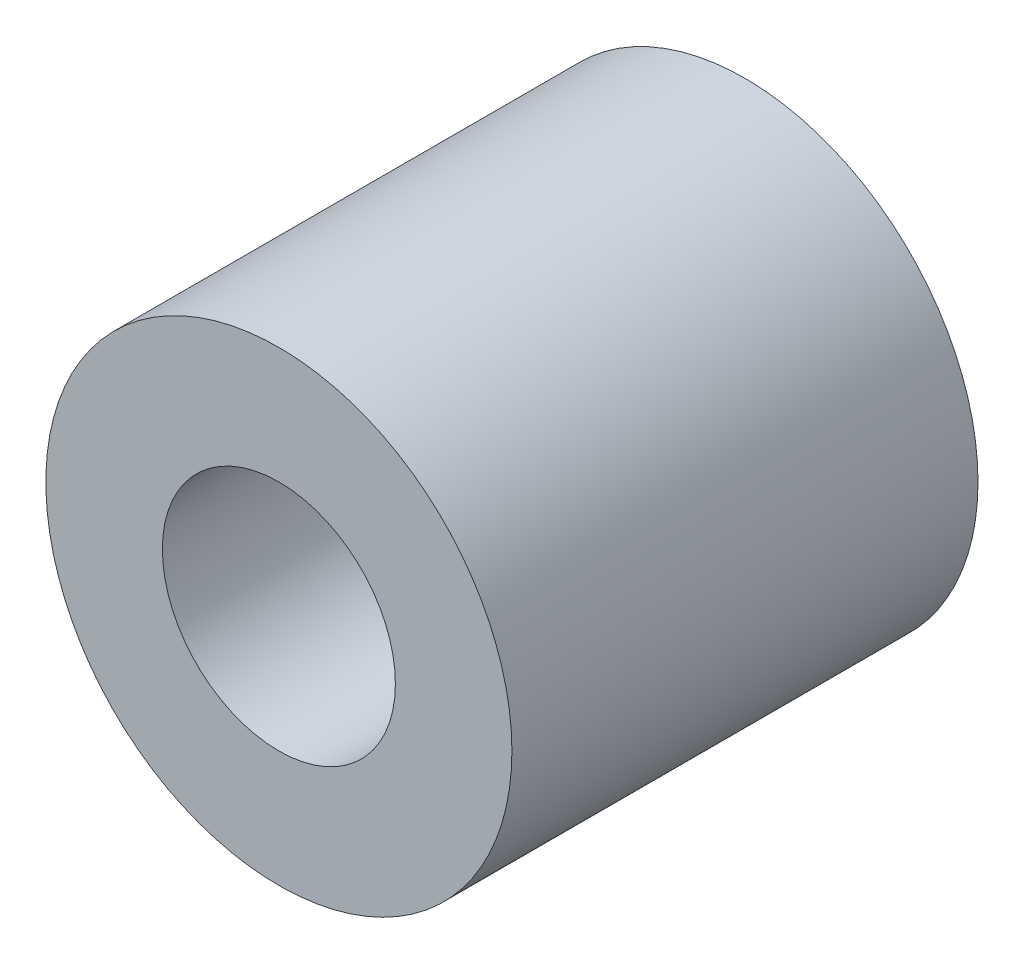
SolidWorks part; units mm, degrees
ref_plane "Top Plane" through (0, 0, 0) normal (0, 0, 1) x (1, 0, 0)
ref_plane "Right Plane" through (0, 0, 0) normal (0, 1, 0) x (1, 0, 0)
ref_plane "Front Plane" through (0, 0, 0) normal (1, 0, 0) x (0, 0, -1)
sketch "Sketch1" plane through (0, 0, 0) normal (0, 0, 1) x (1, 0, 0)
  circle A0 centre (16.35, -29.65) radius 6
  dimension "D1" = 12
extrude "Boss-Extrude1" add sketch "Sketch1" along normal blind 12 from offset 15
sketch "Sketch3" plane through (0, 0, 15) normal (0, 0, -1) x (-1, 0, 0)
  line L0 (-18.35, -32.0185) -> (-18.35, -27.2815) construction
  line L1 (-18.35, -32.0185) -> (-18.35, -27.2815)
  arc A0 (-18.35, -32.0185) -> (-18.35, -27.2815) centre (-16.35, -29.65) ccw construction
  arc A3 (-18.35, -32.0185) -> (-18.35, -27.2815) centre (-16.35, -29.65) ccw
extrude "Cut-Extrude2" cut sketch "Sketch3" against normal blind 6
sketch "Sketch2" plane through (0, 0, 27) normal (0, 0, 1) x (1, 0, 0)
  circle A0 centre (16.35, -29.65) radius 3
  arc A1 (18.35, -27.2815) -> (18.35, -32.0185) centre (16.35, -29.65) ccw construction
  dimension "D1" = 6
extrude "Cut-Extrude1" cut sketch "Sketch2" against normal blind 6
